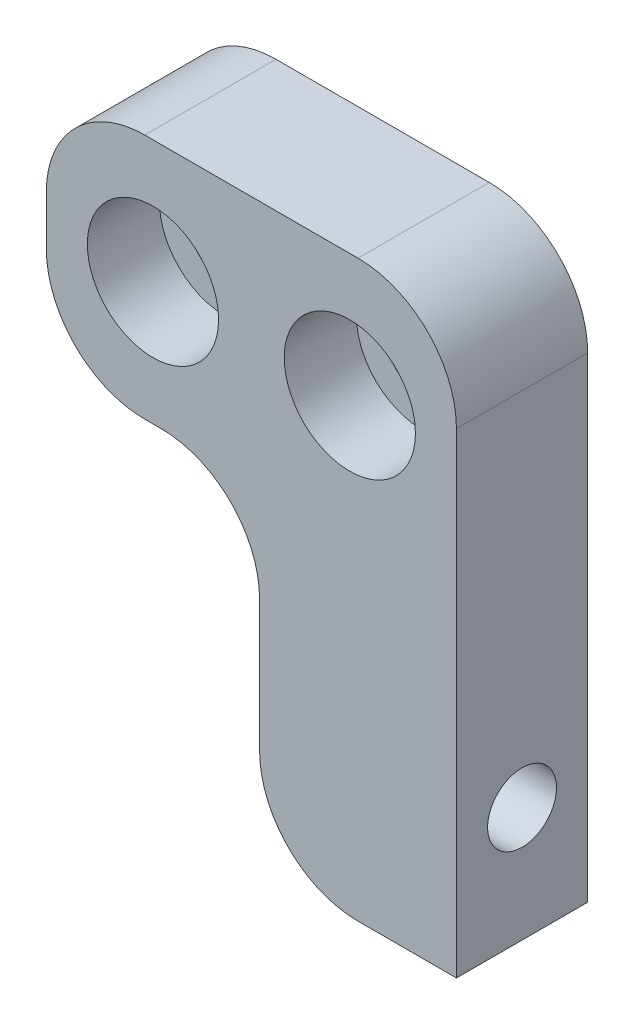
SolidWorks part; units mm, degrees
material "1023 Листовая углеродистая сталь (SS)"
ref_plane "Front" through (0, 0, 0) normal (0, 0, 1) x (1, 0, 0)
ref_plane "Top" through (0, 0, 0) normal (0, 1, 0) x (1, 0, 0)
ref_plane "Right" through (0, 0, 0) normal (1, 0, 0) x (0, 0, -1)
sketch "Sketch1" plane through (0, 0, 0) normal (0, 0, 1) x (1, 0, 0)
  line L7 (0, 6) -> (0, 14)
  line L8 (-6, 20) -> (-7, 20)
  line L9 (-13, 26) -> (-13, 29)
  line L10 (-7, 35) -> (6, 35)
  line L11 (12, 29) -> (12, 0)
  line L12 (12, 0) -> (6, 0)
  arc A0 (0, 6) -> (6, 0) centre (6, 6) ccw
  arc A1 (0, 14) -> (-6, 20) centre (-6, 14) ccw
  arc A2 (-7, 20) -> (-13, 26) centre (-7, 26) cw
  arc A3 (6, 35) -> (12, 29) centre (6, 29) cw
  arc A4 (-13, 29) -> (-7, 35) centre (-7, 29) cw
  point P9 (0, 0)
  point P13 (0, 20)
  point P16 (-13, 20)
  point P19 (12, 35)
  point P22 (-13, 35)
  dimension "D5" = 6
  dimension "D1" = 20
  dimension "D2" = 13
  dimension "D3" = 15
  dimension "D4" = 25
extrude "Extrude1" add sketch "Sketch1" along normal blind 8
hole_wizard "CBORE for M4 Hex Socket Head Cap Screw1" positions "Sketch2" profile "Sketch3" counterbore size "M4" standard "DIN" end condition through all
sketch "Sketch2" plane through (0, 0, 8) normal (0, 0, 1) x (1, 0, 0)
  line L0 (-6.5, 27.5) -> (5.5, 27.5)
  line L2 (-0.5, 27.5) -> (-0.5, 35)
  line L3 (6, 35) -> (-7, 35) construction
  point P0 (-6.5, 27.5)
  point P2 (5.5, 27.5)
  dimension "D1" = 12
  dimension "D2" = 7.5
sketch "Sketch3" plane through (-6.5, 27.5, 8) normal (1, 0, 0) x (0, -1, 0)
  line L0 (0, 0) -> (0, 8)
  line L1 (0, 8) -> (2.25, 8)
  line L3 (2.25, 8) -> (2.25, 4.4)
  line L4 (2.25, 4.4) -> (4, 4.4)
  line L5 (4, 4.4) -> (4, 0)
  line L7 (4, 0) -> (0, 0)
  line L11 (0, -6.35) -> (0, 107.95) construction
  dimension "Диаметр сквозного отверстия" = 4.5
  dimension "Глубина сквозного отверстия" = 8
  dimension "Диаметр цековки" = 8
  dimension "Глубина цековки" = 4.4
hole_wizard "M5 Tapped Hole1" positions "Sketch4" profile "Sketch5" tap size "M5" standard "DIN" end condition through all
sketch "Sketch4" plane through (12, 0, 0) normal (1, 0, 0) x (0, 0, -1)
  line L0 (-8, 0) -> (0, 0) construction
  line L1 (-4, 7) -> (-4, 0)
  point P0 (-4, 7)
  dimension "D1" = 7
sketch "Sketch5" plane through (12, 7, 4) normal (0, 1, 0) x (0, 0, -1)
  line L0 (0, 0) -> (0, 25)
  line L1 (0, 25) -> (2.1, 25)
  line L2 (2.1, 25) -> (2.1, 0)
  line L5 (2.1, 0) -> (0, 0)
  line L11 (0, -6.35) -> (0, 107.95) construction
  dimension "Диаметр проходного сверла" = 4.2
  dimension "Глубина проходного сверла" = 25
cosmetic thread "Cosmetic Thread1"
